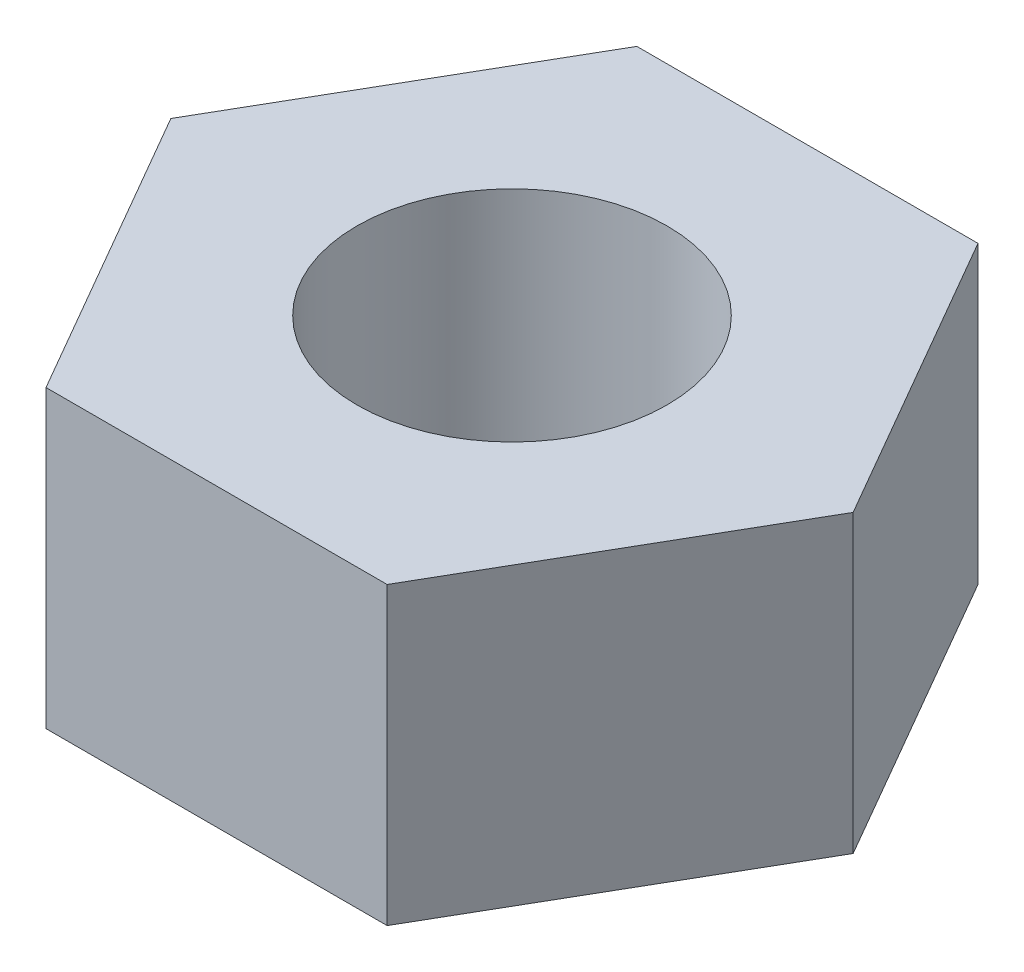
SolidWorks part; units mm, degrees
material "acero"
ref_plane "Alzado" through (0, 0, 0) normal (0, 0, 1) x (1, 0, 0)
ref_plane "Planta" through (0, 0, 0) normal (0, 1, 0) x (1, 0, 0)
ref_plane "Vista lateral" through (0, 0, 0) normal (1, 0, 0) x (0, 0, -1)
sketch "Croquis1" plane through (0, 0, 0) normal (0, 1, 0) x (1, 0, 0)
  line L1 (-2.3094, 4) -> (-4.6188, 0)
  line L2 (-4.6188, 0) -> (-2.3094, -4)
  line L3 (-2.3094, -4) -> (2.3094, -4)
  line L4 (2.3094, -4) -> (4.6188, 0)
  line L5 (4.6188, 0) -> (2.3094, 4)
  line L6 (2.3094, 4) -> (-2.3094, 4)
  circle A0 centre (0, 0) radius 4 construction
  circle A1 centre (0, 0) radius 2.1
  dimension "D1" = 4.2
  dimension "D2" = 8
extrude "Saliente-Extruir1" add sketch "Croquis1" along normal blind 4
